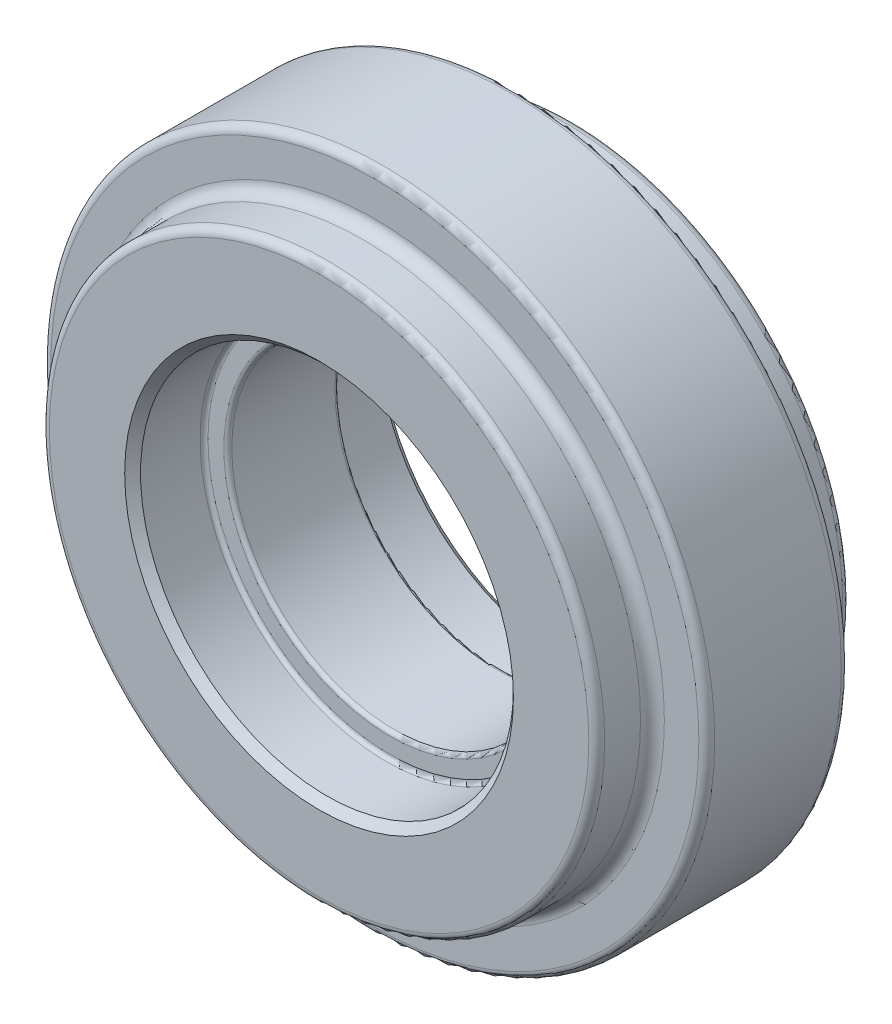
SolidWorks part; units mm, degrees
material "AISI 1045 钢，冷拔"
ref_plane "前视基准面" through (0, 0, 0) normal (0, 0, 1) x (1, 0, 0)
ref_plane "上视基准面" through (0, 0, 0) normal (0, 1, 0) x (1, 0, 0)
ref_plane "右视基准面" through (0, 0, 0) normal (1, 0, 0) x (0, 0, -1)
sketch "草图1" plane through (0, 0, 0) normal (0, 0, 1) x (1, 0, 0)
  circle A0 centre (0, 0) radius 51.3726 construction
  circle A1 centre (0, 0) radius 41.8476
  dimension "D1" = 102.7452
  dimension "D2" = 9.525
extrude "凸台-拉伸1" add sketch "草图1" along normal blind 17.955
sketch "草图2" plane through (0, 0, 17.955) normal (0, 0, 1) x (1, 0, 0)
  circle A0 centre (0, 0) radius 35
  dimension "D1" = 70
extrude "凸台-拉伸2" add sketch "草图2" along normal blind 7.0225
sketch "草图3" plane through (0, 0, 0) normal (0, 0, -1) x (-1, 0, 0)
  circle A2 centre (0, 0) radius 35 construction
  circle A3 centre (0, 0) radius 35
extrude "凸台-拉伸3" add sketch "草图3" along normal blind 7.0225
fillet "圆角1" radius 1.5 2 edges at (-35, 0, 0) (35, 0, 17.955)
fillet "圆角2" radius 1 4 edges at (-35, 0, -7.0225) (41.8476, 0, 0) (41.8476, 0, 17.955) (35, 0, 24.9775)
sketch "草图4" plane through (0, 0, 24.9775) normal (0, 0, 1) x (1, 0, 0)
  circle A0 centre (0, 0) radius 23.5
  dimension "D1" = 47
extrude "切除-拉伸1" cut sketch "草图4" against normal blind 9
sketch "草图5" plane through (0, 0, -7.0225) normal (0, 0, -1) x (-1, 0, 0)
  circle A0 centre (0, 0) radius 23.5 construction
  circle A1 centre (0, 0) radius 23.5
extrude "切除-拉伸2" cut sketch "草图5" against normal blind 9
sketch "草图6" plane through (0, 0, 1.9775) normal (0, 0, -1) x (-1, 0, 0)
  circle A2 centre (0, 0) radius 20.5
  circle A3 centre (0, 0) radius 20.5
  dimension "D1" = 3
extrude "切除-拉伸3" cut sketch "草图6" against normal up to next
fillet "圆角3" radius 0.5 4 edges at (-23.5, 0, 1.9775) (-20.5, 0, 1.9775) (20.5, 0, 15.9775) (23.5, 0, 15.9775)
chamfer "倒角1" distance 1 angle 45 2 edges at (23.5, 0, 24.9775) (-23.5, 0, -7.0225)
